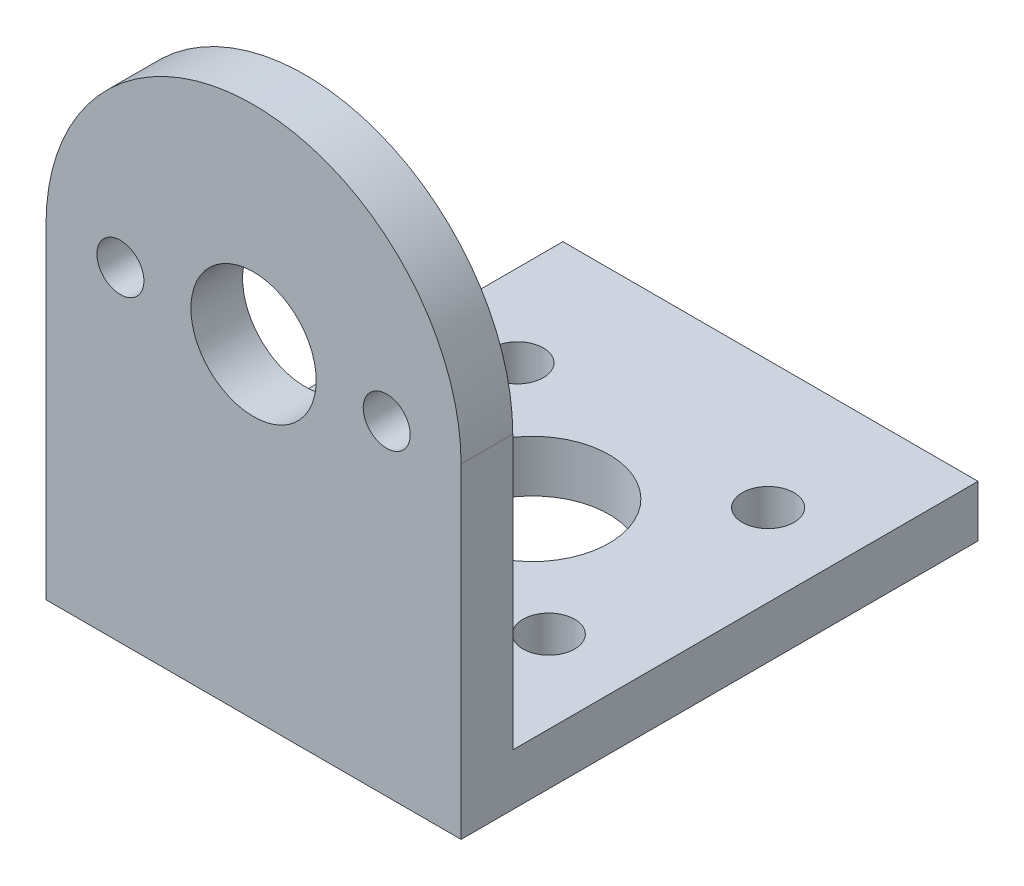
SolidWorks part; units mm, degrees
ref_plane "前视基准面" through (0, 0, 0) normal (0, 0, 1) x (1, 0, 0)
ref_plane "上视基准面" through (0, 0, 0) normal (0, 1, 0) x (1, 0, 0)
ref_plane "右视基准面" through (0, 0, 0) normal (1, 0, 0) x (0, 0, -1)
sketch "草图1" plane through (0, 0, 0) normal (0, 0, 1) x (1, 0, 0)
  line L0 (0, -18.15) -> (0, 18.15) construction
  line L2 (-13.25, 0) -> (-13.25, -20.75)
  line L3 (-13.25, -20.75) -> (13.25, -20.75)
  line L4 (13.25, 0) -> (13.25, -20.75)
  arc A1 (-13.25, 0) -> (13.25, 0) centre (0, 0) cw
  circle A2 centre (0, 0) radius 4
  circle A3 centre (-8.5, 0) radius 1.5
  circle A4 centre (8.5, 0) radius 1.5
  dimension "D1" = 26.5
  dimension "D3" = 8
  dimension "D4" = 3
  dimension "D5" = 8.5
  dimension "D6" = 13.25
  dimension "D2" = 20.75
extrude "凸台-拉伸1" add sketch "草图1" along normal blind 3.3
sketch "草图2" plane through (0, 0, 0) normal (0, 0, 1) x (1, 0, 0)
  line L0 (-13.25, 0) -> (-13.25, -20.75) construction
  line L1 (13.25, -20.75) -> (-13.25, -20.75)
  line L2 (13.25, -20.75) -> (13.25, -17.45)
  line L3 (13.25, -17.45) -> (-13.25, -17.45)
  line L4 (-13.25, -20.75) -> (-13.25, -17.45)
  dimension "D1" = 3.3
extrude "凸台-拉伸2" add sketch "草图2" against normal blind 29.7
sketch "草图3" plane through (0, -17.45, 0) normal (0, 1, 0) x (1, 0, 0)
  line L0 (13.25, 29.7) -> (-13.25, 29.7) construction
  line L1 (-13.25, 29.7) -> (-13.25, 0) construction
  line L2 (0, 14.5) -> (0, 0) construction
  line L3 (0, -18.15) -> (0, 18.15) construction
  circle A0 centre (0, 14.5) radius 4.9
  circle A1 centre (-8, 21.55) radius 1.65
  circle A2 centre (-8, 7.55) radius 1.65
  circle A3 centre (8, 7.55) radius 1.65
  circle A4 centre (8, 21.55) radius 1.65
  dimension "D1" = 9.8
  dimension "D2" = 15.2
  dimension "D3" = 8.15
  dimension "D4" = 3.3
  dimension "D6" = 3.3
  dimension "D7" = 14
  dimension "D8" = 5.25
  dimension "D5" = 5.25
extrude "切除-拉伸1" cut sketch "草图3" against normal up to surface (3.3 mm away) up to face at (0, -20.75, -13.2)
